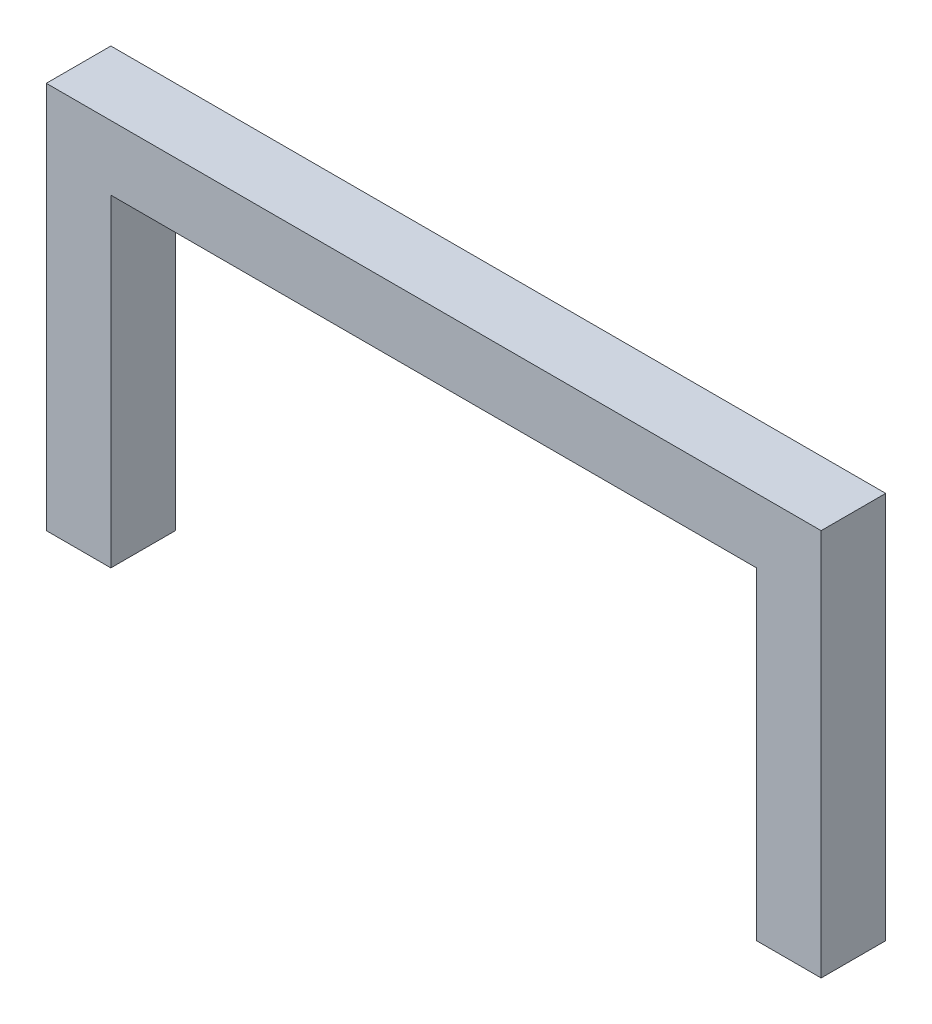
SolidWorks part; units mm, degrees
ref_plane "Front Plane" through (0, 0, 0) normal (0, 0, 1) x (1, 0, 0)
ref_plane "Top Plane" through (0, 0, 0) normal (0, 1, 0) x (1, 0, 0)
ref_plane "Right Plane" through (0, 0, 0) normal (1, 0, 0) x (0, 0, -1)
sketch "Sketch1" plane through (0, 0, 0) normal (0, 0, 1) x (1, 0, 0)
  line L0 (-3.175, 0) -> (-3.175, 19.05)
  line L2 (0, 0) -> (0, 15.875)
  line L3 (0, 15.875) -> (31.75, 15.875)
  line L4 (31.75, 0) -> (31.75, 15.875)
  line L5 (-3.175, 19.05) -> (34.925, 19.05)
  line L6 (34.925, 0) -> (34.925, 19.05)
  line L8 (-3.175, 0) -> (0, 0)
  line L9 (-3.175, -3.175) -> (-3.175, 19.05) construction
  line L10 (-3.175, -3.175) -> (34.925, -3.175) construction
  line L11 (34.925, -3.175) -> (34.925, 19.05) construction
  line L12 (0, 0) -> (31.75, 0) construction
  line L13 (31.75, 0) -> (34.925, 0)
  dimension "D2" = 15.875
  dimension "D3" = 31.75
  dimension "D1" = 3.175
extrude "Boss-Extrude1" add sketch "Sketch1" along normal blind 3.175 contours L0 L5 L6 L13 L4 L3 L2 L8
